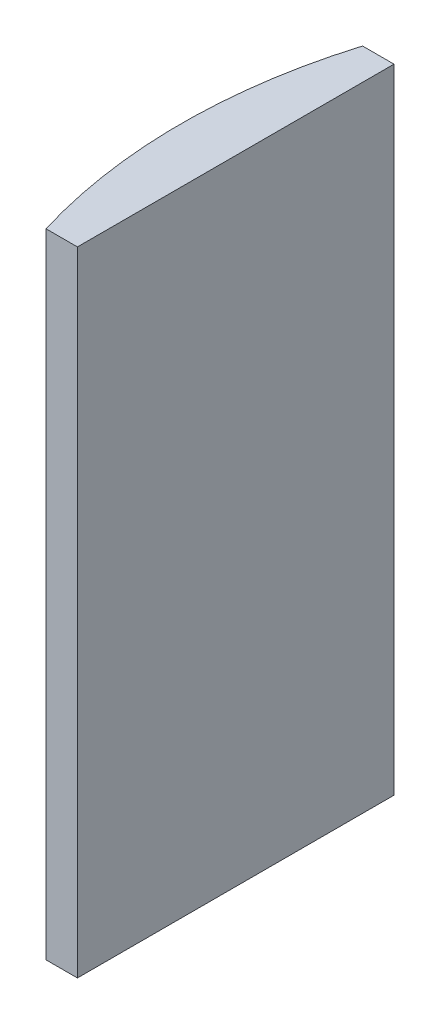
SolidWorks part; units mm, degrees
ref_plane "前视基准面" through (0, 0, 0) normal (0, 0, 1) x (1, 0, 0)
ref_plane "上视基准面" through (0, 0, 0) normal (0, 1, 0) x (1, 0, 0)
ref_plane "右视基准面" through (0, 0, 0) normal (1, 0, 0) x (0, 0, -1)
sketch "草图1" plane through (0, 0, 0) normal (0, 1, 0) x (1, 0, 0)
  line L0 (10.7432, 0) -> (-607.0701, 0) construction
  line L1 (-45.121, 15) -> (-42.1448, 15)
  line L2 (-45.121, -15) -> (-42.1448, -15)
  line L3 (-42.1448, 15) -> (-42.1448, -15)
  arc A0 (-45.121, 15) -> (-45.121, -15) centre (4.3552, 0) ccw
  point P19 (-47.3448, 0)
  point P20 (-42.1448, 0)
  dimension "D2" = 15
  dimension "D3" = 51.7
  dimension "D4" = 5.2
  dimension "D1" = 15
extrude "凸台-拉伸1" add sketch "草图1" along normal blind 60
